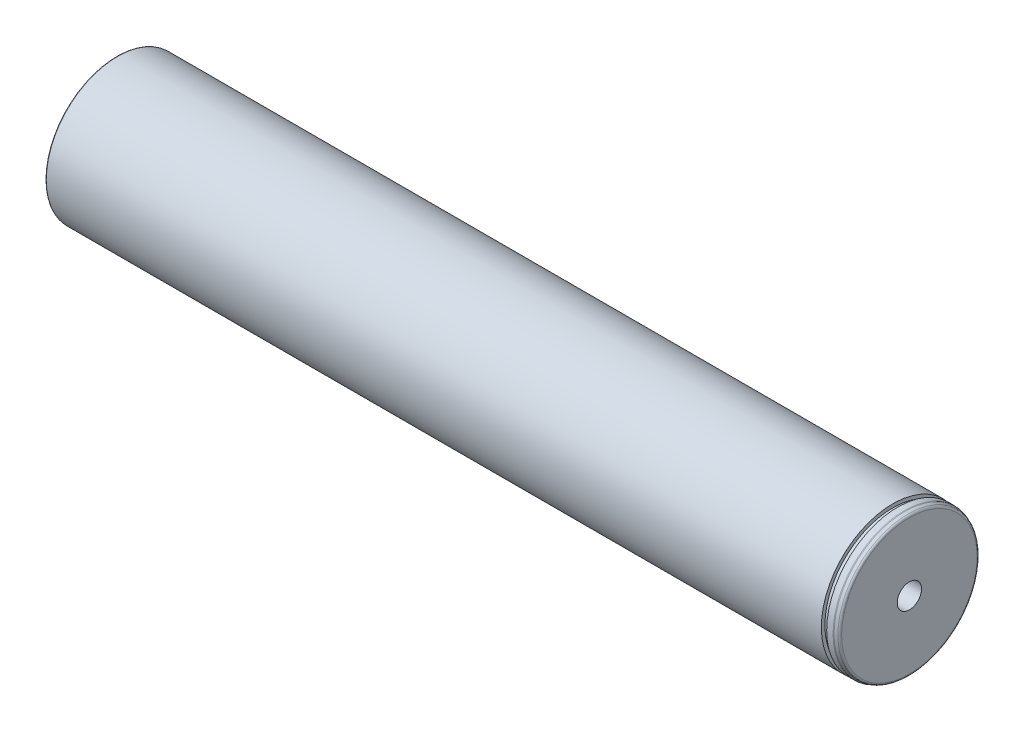
SolidWorks part; units mm, degrees
revolve "Base-Revolve" add sketch "Sketch1" angle 360 about L0
sketch "Sketch1" plane through (0, 0, 0) normal (0, 0, 1) x (1, 0, 0)
  line L0 (-168, 0) -> (170, 0) construction
  line L1 (163, 30) -> (0, 30)
  line L2 (163, 30) -> (163, 28.5)
  line L4 (-145.0555, 0) -> (147.0555, 0)
  line L5 (169.342, 29.4115) -> (168.1657, 29.8397)
  line L6 (-163, 29.6) -> (-163, 28.4)
  line L7 (-168, 5.1) -> (-148, 5.1)
  line L8 (-148, 5.1) -> (-145.0555, 0)
  line L9 (170, 5.1) -> (150, 5.1)
  line L10 (150, 5.1) -> (147.0555, 0)
  line L13 (0, 30) -> (-162.6, 30)
  line L17 (-164.2, 24.8845) -> (-167.8, 22.8061)
  line L19 (-164, 28) -> (-164, 25.2309)
  line L20 (-168, 22.4597) -> (-168, 5.1)
  line L21 (-163.4, 28) -> (-164, 28)
  line L22 (170, 28.4719) -> (170, 5.1)
  line L23 (165.15, 29.9) -> (167.8237, 29.9)
  line L24 (165.15, 28.5) -> (165.15, 29.9)
  line L25 (163, 28.5) -> (165.15, 28.5)
  arc A0 (170, 28.4719) -> (169.342, 29.4115) centre (169, 28.4719) ccw
  arc A1 (-163.4, 28) -> (-163, 28.4) centre (-163.4, 28.4) ccw
  arc A2 (167.8237, 29.9) -> (168.1657, 29.8397) centre (167.8237, 28.9) cw
  arc A3 (-167.8, 22.8061) -> (-168, 22.4597) centre (-167.6, 22.4597) ccw
  arc A4 (-164.2, 24.8845) -> (-164, 25.2309) centre (-164.4, 25.2309) ccw
  arc A5 (-163, 29.6) -> (-162.6, 30) centre (-162.6, 29.6) cw
  point P15 (168, 29.9)
  point P28 (-164, 25)
  point P31 (-163, 30)
  dimension "D11" = 50
  dimension "D6" = 2
  dimension "D16" = 20
  dimension "D17" = 1
  dimension "D19" = 0.4
  dimension "D2" = 59.8
  dimension "D3" = 57
  dimension "D4" = 2.15
  dimension "D5" = 7
  dimension "D7" = 5
  dimension "D8" = 1
  dimension "D9" = 56
  dimension "D10" = 30
  dimension "D12" = 60
  dimension "D13" = 163
  dimension "D14" = 326
  dimension "D20" = 10.2
  dimension "D21" = 20
  dimension "D22" = 60
  dimension "D23" = 10.2
  dimension "D24" = 20
  dimension "D25" = 60
cosmetic thread "Cosmetic Thread1"
cosmetic thread "Cosmetic Thread2"
ref_plane "Front" through (0, 0, 0) normal (0, 0, 1) x (1, 0, 0)
ref_plane "Top" through (0, 0, 0) normal (0, 1, 0) x (1, 0, 0)
ref_plane "Right" through (0, 0, 0) normal (1, 0, 0) x (0, 0, -1)
